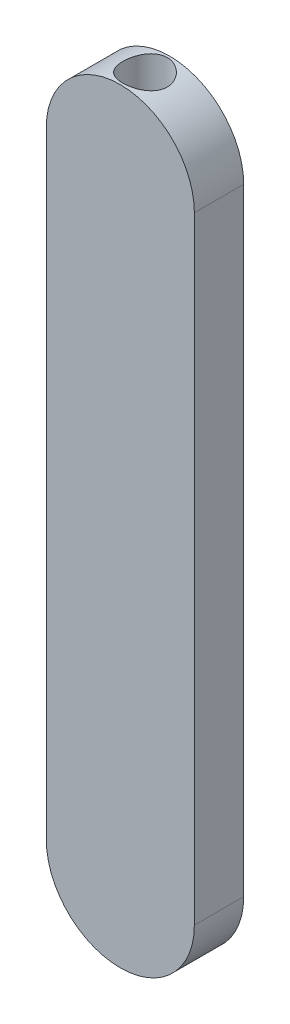
SolidWorks part; units mm, degrees
ref_plane "Front Plane" through (0, 0, 0) normal (0, 0, 1) x (1, 0, 0)
ref_plane "Top Plane" through (0, 0, 0) normal (0, 1, 0) x (1, 0, 0)
ref_plane "Right Plane" through (0, 0, 0) normal (1, 0, 0) x (0, 0, -1)
sketch "Sketch3" plane through (0, 0, 0) normal (0, 0, 1) x (1, 0, 0)
  line L2 (-30, -125) -> (-30, 125)
  line L4 (30, -125) -> (30, 125)
  line L5 (-30, -125) -> (30, 125) construction
  line L6 (-30, 125) -> (30, -125) construction
  arc A0 (30, 125) -> (-30, 125) centre (0, 125) ccw
  arc A1 (-30, -125) -> (30, -125) centre (0, -125) ccw
  point P0 (0, 0)
  dimension "D1" = 250
  dimension "D2" = 60
extrude "Boss-Extrude1" add sketch "Sketch3" along normal mid plane 20
ref_plane "Plane1" through (0, 125, 0) normal (0, 1, 0) x (1, 0, 0)
sketch "Sketch5" plane through (0, 125, 0) normal (0, 1, 0) x (1, 0, 0)
  circle A0 centre (0, 0) radius 9
  dimension "D1" = 18
extrude "Cut-Extrude1" cut sketch "Sketch5" along normal blind 40
